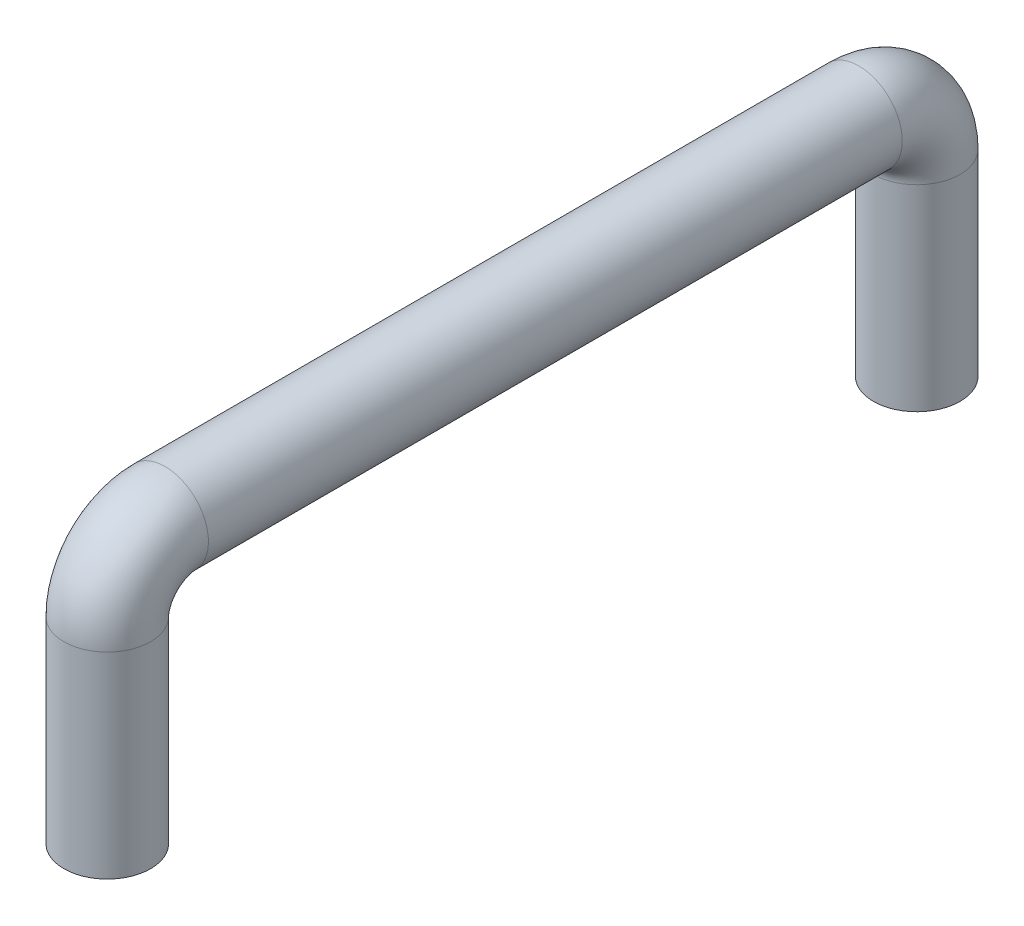
SolidWorks part; units mm, degrees
ref_plane "Front" through (0, 0, 0) normal (0, 0, 1) x (1, 0, 0)
ref_plane "Top" through (0, 0, 0) normal (0, 1, 0) x (1, 0, 0)
ref_plane "Right" through (0, 0, 0) normal (1, 0, 0) x (0, 0, -1)
sketch "Sketch1" plane through (0, 0, 0) normal (1, 0, 0) x (0, 0, -1)
  line L0 (0, 0) -> (0, 21.59)
  line L1 (6.35, 27.94) -> (82.55, 27.94)
  line L2 (88.9, 21.59) -> (88.9, 0)
  arc A0 (0, 21.59) -> (6.35, 27.94) centre (6.35, 21.59) cw
  arc A1 (82.55, 27.94) -> (88.9, 21.59) centre (82.55, 21.59) cw
  point P6 (0, 27.94)
  point P9 (88.9, 27.94)
  dimension "D3" = 6.35
  dimension "D1" = 88.9
  dimension "D2" = 27.94
sketch "Sketch2" plane through (0, 0, 0) normal (0, 1, 0) x (1, 0, 0)
  circle A0 centre (0, 0) radius 4.7625
  dimension "D1" = 9.525
sweep "Base-Sweep" add profiles "Sketch2" path "Sketch1"
sketch "Sketch3" plane through (0, 0, 0) normal (0, -1, 0) x (1, 0, 0)
  circle A0 centre (0, 0) radius 1.7272
  circle A1 centre (0, -88.9) radius 1.7272
  dimension "D1" = 3.4544
extrude "Cut-Extrude1" cut sketch "Sketch3" against normal blind 12.7
